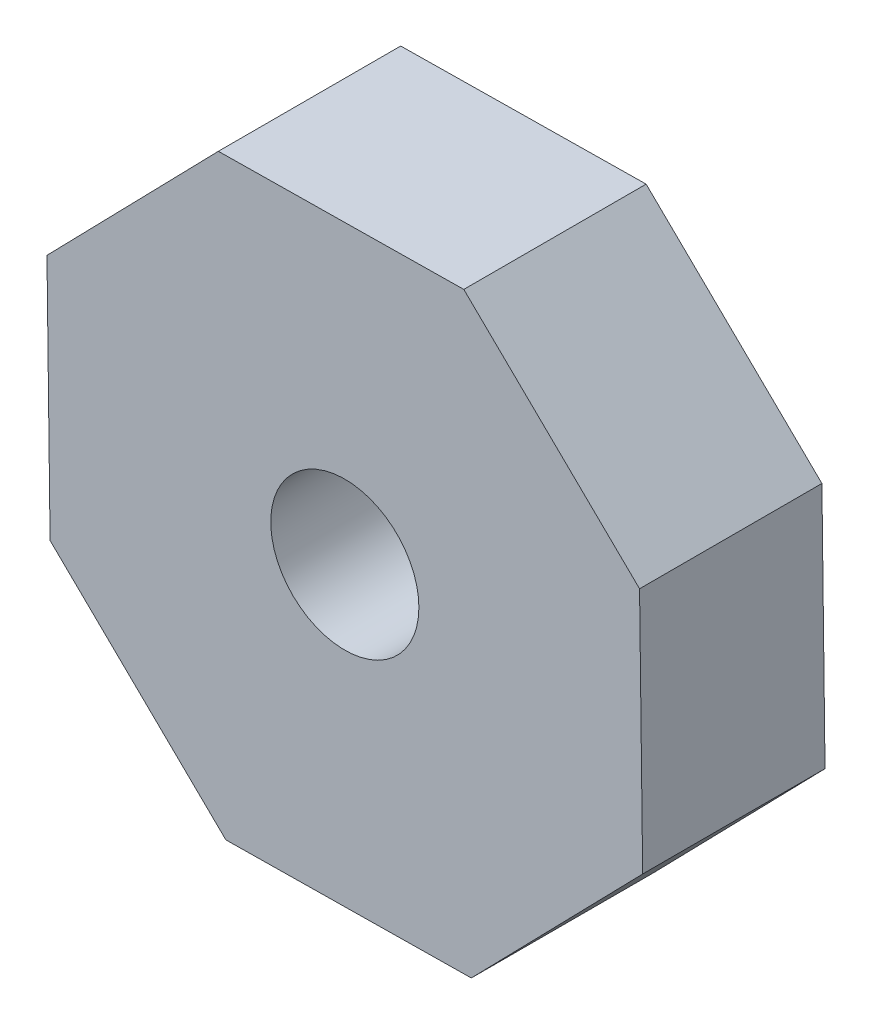
SolidWorks part; units mm, degrees
ref_plane "Front Plane" through (0, 0, 0) normal (0, 0, 1) x (1, 0, 0)
ref_plane "Top Plane" through (0, 0, 0) normal (0, 1, 0) x (1, 0, 0)
ref_plane "Right Plane" through (0, 0, 0) normal (1, 0, 0) x (0, 0, -1)
sketch "Sketch1" plane through (0, 0, 0) normal (0, 0, 1) x (1, 0, 0)
  line L1 (6.4653, 2.7746) -> (2.6097, 6.5336)
  line L2 (2.6097, 6.5336) -> (-2.7746, 6.4653)
  line L3 (-2.7746, 6.4653) -> (-6.5336, 2.6097)
  line L4 (-6.5336, 2.6097) -> (-6.4653, -2.7746)
  line L5 (-6.4653, -2.7746) -> (-2.6097, -6.5336)
  line L6 (-2.6097, -6.5336) -> (2.7746, -6.4653)
  line L7 (2.7746, -6.4653) -> (6.5336, -2.6097)
  line L8 (6.5336, -2.6097) -> (6.4653, 2.7746)
  circle A0 centre (0, 0) radius 6.5 construction
  dimension "D1" = 6.5
extrude "Boss-Extrude1" add sketch "Sketch1" along normal blind 4
sketch "Sketch2" plane through (0, 0, 4) normal (0, 0, 1) x (1, 0, 0)
  circle A0 centre (0, 0) radius 1.625
  dimension "D1" = 3.25
extrude "Cut-Extrude1" cut sketch "Sketch2" against normal through all
